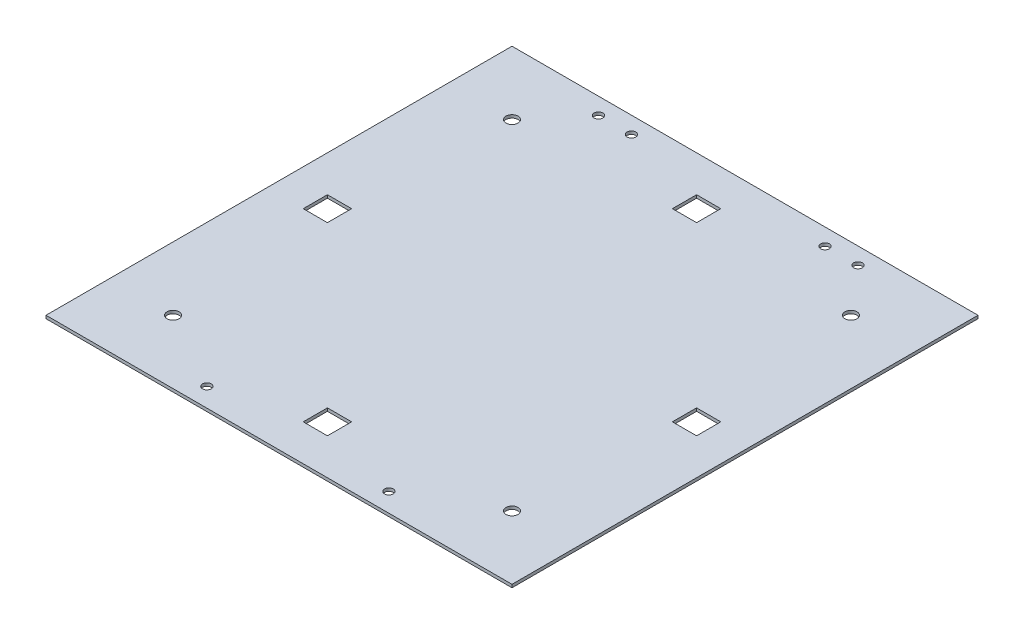
SolidWorks part; units mm, degrees
ref_plane "Front Plane" through (0, 0, 0) normal (0, 0, 1) x (1, 0, 0)
ref_plane "Top Plane" through (0, 0, 0) normal (0, 1, 0) x (1, 0, 0)
ref_plane "Right Plane" through (0, 0, 0) normal (1, 0, 0) x (0, 0, -1)
sketch "Sketch1" plane through (0, 0, 0) normal (0, 1, 0) x (1, 0, 0)
  line L1 (0, 0) -> (244.475, 0)
  line L2 (0, 0) -> (0, 244.475)
  line L3 (0, 244.475) -> (244.475, 244.475)
  line L4 (244.475, 0) -> (244.475, 244.475)
  dimension "D2" = 244.475
extrude "Main Body" add sketch "Sketch1" along normal blind 1.5875
sketch "Sketch2" plane through (0, 1.5875, 0) normal (0, 1, 0) x (1, 0, 0)
  line L0 (56.4515, 235.6866) -> (69.1515, 235.6866) construction
  line L1 (175.3235, 235.6866) -> (188.0235, 235.6866) construction
  line L2 (244.475, 244.475) -> (0, 244.475) construction
  line L3 (0, 0) -> (244.475, 0) construction
  line L6 (0, 0) -> (244.475, 0) construction
  circle A0 centre (54.1655, 235.6866) radius 2.286
  circle A1 centre (71.4375, 235.6866) radius 2.286
  circle A2 centre (173.0375, 235.6866) radius 2.286
  circle A3 centre (190.3095, 235.6866) radius 2.286
  circle A4 centre (74.4855, 9.906) radius 2.286
  circle A5 centre (169.9895, 9.906) radius 2.286
  point P14 (122.2375, 244.475)
  point P19 (122.2375, 0)
  point P25 (122.2375, 0)
  dimension "D3" = 4.572
  dimension "D7" = 4.572
  dimension "D10" = 47.752
  dimension "D9" = 47.752
  dimension "D1" = 12.7
  dimension "D2" = 12.7
  dimension "D4" = 8.7884
  dimension "D5" = 50.8
  dimension "D6" = 50.8
  dimension "D8" = 9.906
extrude "Hinges/Lock Holes" cut sketch "Sketch2" against normal through all
sketch "Sketch3" plane through (0, 1.5875, 0) normal (0, 1, 0) x (1, 0, 0)
  line L0 (244.475, 0) -> (0, 244.475) construction
  line L5 (244.475, 0) -> (244.475, 244.475) construction
  line L6 (211.1375, 33.3375) -> (33.3375, 33.3375) construction
  line L7 (211.1375, 33.3375) -> (211.1375, 211.1375) construction
  line L8 (211.1375, 211.1375) -> (33.3375, 211.1375) construction
  line L9 (33.3375, 33.3375) -> (33.3375, 211.1375) construction
  circle A6 centre (211.1375, 33.3375) radius 3.175
  circle A7 centre (33.3375, 211.1375) radius 3.175
  circle A8 centre (211.1375, 211.1375) radius 3.175
  circle A9 centre (33.3375, 33.3375) radius 3.175
  point P7 (244.475, 122.2375)
  point P10 (122.2375, 122.2375)
  point P11 (211.1375, 122.2375)
  dimension "D1" = 177.8
  dimension "D2" = 6.35
extrude "Thread Holes" cut sketch "Sketch3" against normal through all
sketch "Sketch4" plane through (0, 1.5875, 0) normal (0, 1, 0) x (1, 0, 0)
  line L0 (0, 0) -> (244.475, 244.475) construction
  line L1 (115.8875, 31.75) -> (128.5875, 31.75)
  line L2 (115.8875, 31.75) -> (115.8875, 19.05)
  line L3 (115.8875, 19.05) -> (128.5875, 19.05)
  line L4 (128.5875, 31.75) -> (128.5875, 19.05)
  line L5 (0, 0) -> (244.475, 0) construction
  line L6 (31.75, 128.5875) -> (19.05, 128.5875)
  line L7 (31.75, 128.5875) -> (31.75, 115.8875)
  line L8 (31.75, 115.8875) -> (19.05, 115.8875)
  line L9 (19.05, 128.5875) -> (19.05, 115.8875)
  line L10 (128.5875, 212.725) -> (128.5875, 225.425)
  line L11 (128.5875, 212.725) -> (115.8875, 212.725)
  line L12 (115.8875, 212.725) -> (115.8875, 225.425)
  line L13 (128.5875, 225.425) -> (115.8875, 225.425)
  line L14 (212.725, 115.8875) -> (225.425, 115.8875)
  line L15 (212.725, 115.8875) -> (212.725, 128.5875)
  line L16 (212.725, 128.5875) -> (225.425, 128.5875)
  line L17 (225.425, 115.8875) -> (225.425, 128.5875)
  line L18 (0, 244.475) -> (0, 0) construction
  point P8 (122.2375, 122.2375)
  point P9 (122.2375, 19.05)
  point P12 (122.2375, 0)
  point P15 (19.05, 122.2375)
  point P28 (0, 122.2375)
  dimension "D1" = 12.7
  dimension "D2" = 12.7
  dimension "D3" = 19.05
  dimension "D5" = 19.05
  dimension "D4" = 4
extrude "LED Holes" cut sketch "Sketch4" against normal through all
